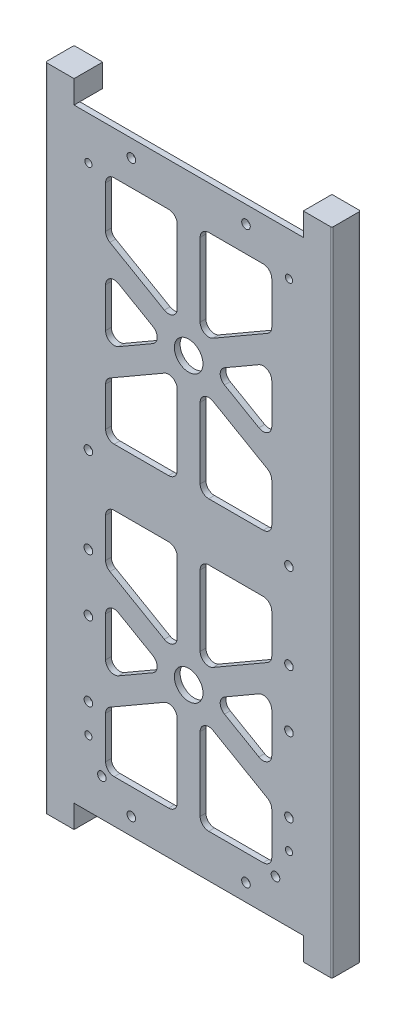
SolidWorks part; units mm, degrees
material "6061-T6 (SS)"
ref_plane "Front Plane" through (0, 0, 0) normal (0, 0, 1) x (1, 0, 0)
ref_plane "Top Plane" through (0, 0, 0) normal (0, 1, 0) x (1, 0, 0)
ref_plane "Right Plane" through (0, 0, 0) normal (1, 0, 0) x (0, 0, -1)
sketch "Sketch1" plane through (0, 0, 0) normal (0, 0, 1) x (1, 0, 0)
  line L1 (0, 0) -> (88, 0)
  line L2 (0, 0) -> (0, 211)
  line L3 (0, 211) -> (88, 211)
  line L4 (88, 0) -> (88, 211)
  dimension "D1" = 88
  dimension "D2" = 211
extrude "Boss-Extrude1" add sketch "Sketch1" along normal blind 2
sketch "Sketch2" plane through (0, 0, 2) normal (0, 0, 1) x (1, 0, 0)
  line L0 (0, 105.5) -> (88, 105.5) construction
  line L1 (0, 211) -> (0, 0) construction
  line L2 (88, 0) -> (88, 211) construction
  line L3 (44, 211) -> (44, 0) construction
  line L4 (88, 211) -> (0, 211) construction
  line L5 (0, 0) -> (88, 0) construction
  line L6 (0, 155.25) -> (88, 155.25) construction
  line L7 (0, 55.75) -> (88, 55.75) construction
  dimension "D1" = 55.75
  dimension "D2" = 55.75
sketch "Sketch3" plane through (0, 0, 2) normal (0, 0, 1) x (1, 0, 0)
  line L0 (0, 155.25) -> (88, 155.25) construction
  line L2 (0, 211) -> (0, 0) construction
  line L3 (15, 196) -> (73, 196)
  line L4 (15, 196) -> (15, 115.5)
  line L5 (15, 115.5) -> (73, 115.5)
  line L6 (73, 196) -> (73, 115.5)
  line L7 (88, 211) -> (0, 211) construction
  line L8 (88, 0) -> (88, 211) construction
  line L9 (0, 105.5) -> (88, 105.5) construction
  line L10 (40, 196) -> (40, 115.5)
  line L11 (48, 196) -> (48, 115.5)
  line L12 (44, 211) -> (44, 0) construction
  line L13 (73, 171.9932) -> (15, 138.5068) construction
  line L14 (15, 171.9932) -> (73, 138.5068) construction
  line L15 (73, 176.612) -> (15, 143.1256)
  line L16 (73, 167.3744) -> (15, 133.888)
  line L17 (15, 176.612) -> (73, 143.1256)
  line L18 (15, 167.3744) -> (73, 133.888)
  circle A0 centre (44, 155.25) radius 5
  dimension "D1" = 10
  dimension "D3" = 15
  dimension "D4" = 15
  dimension "D5" = 15
  dimension "D6" = 10
  dimension "D7" = 8
  dimension "D8" = 4
  dimension "D9" = 30
  dimension "D10" = 30
  dimension "D11" = 8
  dimension "D12" = 4
  dimension "D13" = 4
  dimension "D14" = 8
ref_plane "Plane1" through (0, 105.5, 0) normal (0, -1, 0) x (1, 0, 0)
extrude "Cut-Extrude2" cut sketch "Sketch3" against normal blind 2 contours L18 L11 L5 L6 | L10 L16 L4 L5 | L18 L4 L15 | L16 L17 L6 | L15 L6 L3 L11 | L4 L17 L10 L3
sketch "Sketch4" plane through (0, 0, 2) normal (0, 0, 1) x (1, 0, 0)
  line L0 (0, 155.25) -> (88, 155.25) construction
  circle A0 centre (44, 155.25) radius 5
  dimension "D1" = 10
extrude "Cut-Extrude3" cut sketch "Sketch4" against normal through all
mirror "Mirror2" about plane through (0, 105.5, 0) normal (0, -1, 0) of "Cut-Extrude3", "Cut-Extrude2"
fillet "Fillet2" radius 3 44 edges at (73, 67.8744, 1) (73, 43.6256, 1) (52, 55.75, 1) (40, 48.8218, 1) (40, 15, 1) (15, 15, 1) (15, 34.388, 1) (15, 143.1256, 1) (15, 167.3744, 1) (36, 155.25, 1) (15, 115.5, 1) (15, 133.888, 1) (40, 148.3218, 1) (40, 115.5, 1) (48, 196, 1) (73, 196, 1) (48, 162.1782, 1) (73, 115.5, 1) (48, 115.5, 1) (48, 148.3218, 1) (73, 133.888, 1) (15, 196, 1) (40, 196, 1) (40, 162.1782, 1) (15, 176.612, 1) (73, 167.3744, 1) (73, 143.1256, 1) (52, 155.25, 1) (48, 62.6782, 1) (48, 95.5, 1) (73, 95.5, 1) (73, 77.112, 1) (73, 34.388, 1) (73, 15, 1) (48, 15, 1) (48, 48.8218, 1) (40, 62.6782, 1) (15, 77.112, 1) (15, 95.5, 1) (40, 95.5, 1) (15, 43.6256, 1) (15, 67.8744, 1) (36, 55.75, 1) (73, 176.612, 1)
sketch "Sketch5" plane through (0, 0, 2) normal (0, 0, 1) x (1, 0, 0)
  line L0 (88, 0) -> (88, 211) construction
  line L1 (0, 211) -> (0, 0) construction
  line L4 (0, 5.5) -> (88, 5.5) construction
  line L5 (0, 0) -> (88, 0) construction
  line L6 (0, 205.5) -> (88, 205.5) construction
  circle A1 centre (64, 205.5) radius 1.5
  circle A3 centre (64, 5.5) radius 1.5
  circle A4 centre (24, 5.5) radius 1.5
  circle A5 centre (24, 205.5) radius 1.5
  dimension "D5" = 3
  dimension "D2" = 40
  dimension "D3" = 24
  dimension "D1" = 200
  dimension "D4" = 5.5
  dimension "D6" = 3
  dimension "D7" = 40
  dimension "D8" = 24
  dimension "D9" = 3
  dimension "D10" = 24
  dimension "D11" = 24
  dimension "D12" = 3
sketch "Sketch7" plane through (0, 0, 2) normal (0, 0, 1) x (1, 0, 0)
  line L0 (0, 105.5) -> (151.3859, 105.5) construction
  line L5 (0, 211) -> (0, 0) construction
  line L7 (44, 211) -> (44, 0) construction
  line L8 (88, 211) -> (0, 211) construction
  line L9 (0, 0) -> (88, 0) construction
  line L17 (94, 219) -> (84, 219)
  line L53 (88, 0) -> (88, 211)
  line L54 (84, 219) -> (84, 211)
  line L55 (84, 0) -> (88, 0)
  line L56 (94, 0) -> (94, 211)
  line L57 (94, -8) -> (94, 219)
  line L58 (88, 211) -> (0, 211) construction
  line L59 (84, 211) -> (88, 211)
  line L60 (84, -8) -> (84, 0)
  line L61 (94, -8) -> (84, -8)
  line L62 (-6, -8) -> (4, -8)
  line L63 (4, -8) -> (4, 0)
  line L64 (4, 0) -> (0, 0)
  line L65 (0, 0) -> (0, 211)
  line L66 (4, 211) -> (0, 211)
  line L67 (4, 219) -> (4, 211)
  line L68 (-6, 219) -> (4, 219)
  line L69 (-6, -8) -> (-6, 219)
  dimension "D1" = 6
extrude "Boss-Extrude2" add sketch "Sketch7" against normal blind 10
sketch "Sketch53" plane through (0, 0, -8) normal (0, 0, -1) x (-1, 0, 0)
  line L0 (-84, 0) -> (-84, 211)
  line L1 (-84, 211) -> (-90, 211)
  line L2 (-92, 209) -> (-92, 2)
  line L4 (-44, 0) -> (-44, 211)
  line L5 (-4, 0) -> (-84, 0) construction
  line L6 (-84, 211) -> (-4, 211) construction
  line L8 (-90, 0) -> (-84, 0)
  line L9 (4, 209) -> (4, 2)
  line L10 (-4, 211) -> (2, 211)
  line L11 (-4, 0) -> (-4, 211)
  line L12 (2, 0) -> (-4, 0)
  arc A0 (-92, 209) -> (-90, 211) centre (-90, 209) cw
  arc A1 (-90, 0) -> (-92, 2) centre (-90, 2) cw
  arc A2 (4, 209) -> (2, 211) centre (2, 209) ccw
  arc A3 (2, 0) -> (4, 2) centre (2, 2) ccw
  line M9 (-88, 0) -> (-88, 211)
  dimension "D1" = 2
  dimension "D2" = 2
extrude "Cut-Extrude5" cut sketch "Sketch53" against normal blind 8 contours A1 L8 L1 A0 L2 M9 | L12 A3 L9 A2 L10 L11
ref_plane "Plane2" through (44, 0, 0) normal (-1, 0, 0) x (0, 0, 1)
ref_plane "Plane3" through (44, 0, 0) normal (1, 0, 0) x (0, 0, -1)
sketch "Sketch58" plane through (0, 0, 0) normal (0, 0, -1) x (-1, 0, 0)
  line L0 (-4, 0) -> (-84, 0) construction
  line L4 (4, 209) -> (4, 2) construction
  circle A0 centre (-0.7, 13) radius 1.665
  dimension "D1" = 3.33
  dimension "D2" = 4.7
  dimension "D3" = 13
extrude "Cut-Extrude9" cut sketch "Sketch58" against normal blind 1.8 contours A0
mirror "Mirror4" about plane through (44, 0, 0) normal (1, 0, 0) of "Cut-Extrude9"
sketch "Sketch59" plane through (0, -8, 0) normal (0, -1, 0) x (-1, 0, 0)
  line L0 (-94, 8) -> (-94, -2) construction
  line L1 (6, 8) -> (6, -2) construction
  line L2 (-84, 8) -> (-94, 8) construction
  circle A0 centre (-89, 2.4) radius 2
  circle A1 centre (1, 2.4) radius 2
  dimension "D1" = 4
  dimension "D2" = 5
  dimension "D3" = 5
  dimension "D4" = 5.6
extrude "Cut-Extrude10" cut sketch "Sketch59" against normal blind 10
fillet "Fillet3" radius 0.5 4 edges at (-6, 105.5, 2) (-6, 105.5, -8) (94, 105.5, -8) (94, 105.5, 2)
sketch "Sketch60" plane through (0, 0, 2) normal (0, 0, 1) x (1, 0, 0)
  line L0 (44, 211) -> (44, 0) construction
  line L1 (84, 211) -> (4, 211) construction
  line L2 (4, 0) -> (84, 0) construction
  line L3 (-5.5, 219) -> (-5.5, -8) construction
  line L4 (-4, 209) -> (-4, 2) construction
  point P8 (64, 6)
  point P9 (74.3, 13)
  point P10 (79, 23)
  point P11 (79, 33.2)
  point P12 (79, 59.2)
  point P13 (79, 79.2)
  point P14 (9, 196)
  point P15 (9, 79.2)
  point P16 (9, 109.2)
  point P17 (79, 109.2)
  point P18 (9, 59.2)
  point P19 (9, 33.2)
  point P20 (24, 205)
  point P23 (9, 23)
  point P24 (79, 196)
  point P25 (64, 205)
  point P27 (13.7, 13)
  point P28 (24, 6)
  dimension "D1" = 6
  dimension "D2" = 29.5
  dimension "D3" = 15
  dimension "D4" = 14.5
  dimension "D5" = 14.5
  dimension "D6" = 101.8
  dimension "D7" = 131.8
  dimension "D8" = 14.5
  dimension "D9" = 151.8
  dimension "D10" = 14.5
  dimension "D11" = 14.5
  dimension "D12" = 177.8
  dimension "D13" = 188
  dimension "D14" = 14.5
  dimension "D15" = 198
  dimension "D16" = 17.7
  dimension "D17" = 205
  dimension "D18" = 29.5
hole_wizard "Ø3.0mm Dowel Hole1" positions "Sketch61" profile "Sketch62" hole size "Ø3.0" standard "ANSI Metric" end condition through all
sketch "Sketch61" plane through (0, 0, 2) normal (0, 0, 1) x (1, 0, 0)
  point P0 (24, 205)
  point P3 (64, 205)
  point P6 (9, 109.2)
  point P9 (79, 109.2)
  point P12 (9, 79.2)
  point P15 (79, 79.2)
  point P18 (9, 59.2)
  point P21 (79, 59.2)
  point P24 (9, 33.2)
  point P27 (79, 33.2)
  point P30 (13.7, 13)
  point P33 (24, 6)
  point P36 (74.3, 13)
  point P39 (64, 6)
sketch "Sketch62" plane through (24, 205, 2) normal (1, 0, 0) x (0, -1, 0)
  line L0 (0, 0) -> (0, 10)
  line L1 (0, 10) -> (1.5, 10)
  line L2 (1.5, 10) -> (1.5, 0)
  line L5 (1.5, 0) -> (0, 0)
  line L11 (0, -6.35) -> (0, 107.95) construction
  dimension "Thru Hole Dia." = 3
  dimension "Thru Hole Depth" = 10
hole_wizard "Tap Drill for M3x0.5 Tap1" positions "Sketch63" profile "Sketch64" hole size "M3x0.5" standard "ANSI Metric" end condition through all
sketch "Sketch63" plane through (0, 0, 2) normal (0, 0, 1) x (1, 0, 0)
  point P0 (9, 196)
  point P3 (79, 196)
  point P6 (9, 23)
  point P9 (79, 23)
sketch "Sketch64" plane through (9, 196, 2) normal (1, 0, 0) x (0, -1, 0)
  line L0 (0, 0) -> (0, 10)
  line L1 (0, 10) -> (1.25, 10)
  line L2 (1.25, 10) -> (1.25, 0)
  line L5 (1.25, 0) -> (0, 0)
  line L11 (0, -6.35) -> (0, 107.95) construction
  dimension "Thru Hole Dia." = 2.5
  dimension "Thru Hole Depth" = 10
